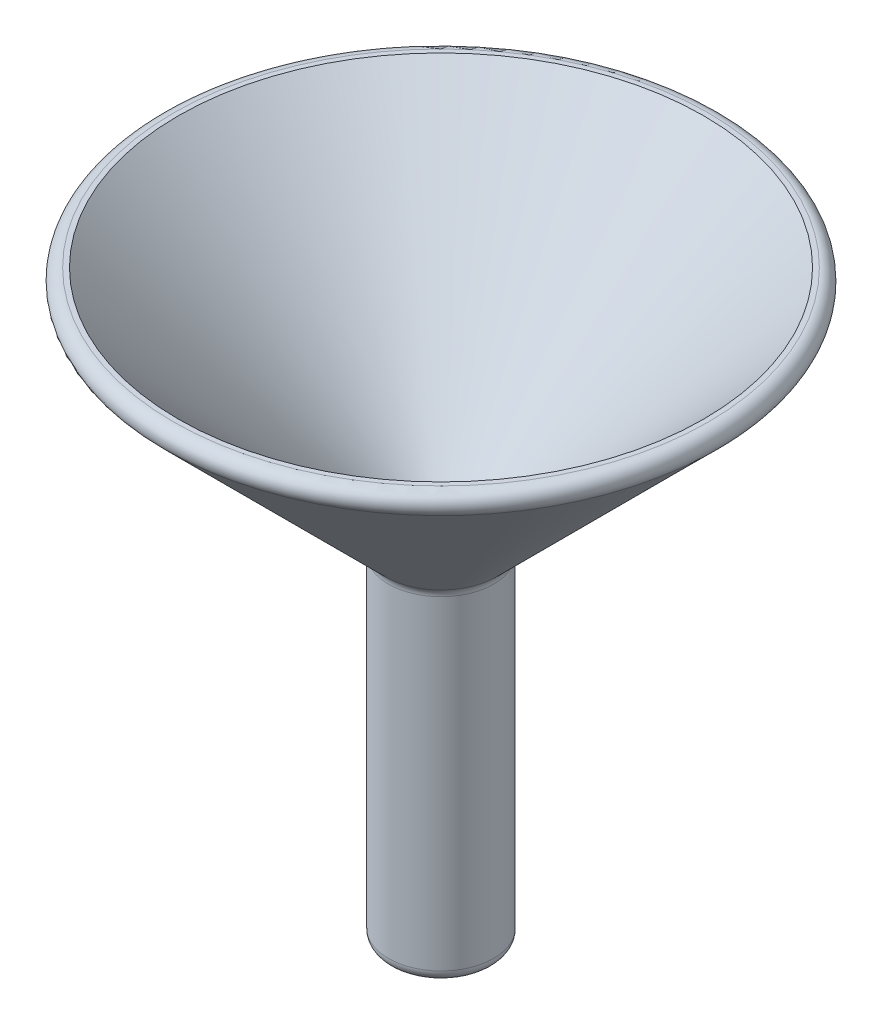
SolidWorks part; units mm, degrees
ref_plane "Спереди" through (0, 0, 0) normal (0, 0, 1) x (1, 0, 0)
ref_plane "Сверху" through (0, 0, 0) normal (0, 1, 0) x (1, 0, 0)
ref_plane "Справа" through (0, 0, 0) normal (1, 0, 0) x (0, 0, -1)
sketch "Эскиз1" plane through (0, 0, 0) normal (0, 0, 1) x (1, 0, 0)
  line L0 (0, 0) -> (0, 1.7212) construction
  line L1 (2.5, 0) -> (2.5, -30)
  line L2 (2.5, 0) -> (22.5, 20)
  line L3 (4.5, -0.8284) -> (4.5, -30)
  line L4 (4.5, -0.8284) -> (25.3284, 20)
  line L5 (4.5, -0.8284) -> (23.9142, 18.5858) construction
  line L6 (22.5, 20) -> (25.3284, 20)
  line L7 (0, 0) -> (23.5511, 0) construction
  line L8 (2.5, -30) -> (4.5, -30)
  dimension "D1" = 5
  dimension "D2" = 30
  dimension "D3" = 2
  dimension "D4" = 135
  dimension "D5" = 45
revolve "Повернуть1" add sketch "Эскиз1" angle 360 about L0
fillet "Скругление1" radius 1 3 edges at (0, 20, -25.3284) (0, -0.8284, -4.5) (0, -30, -4.5)
